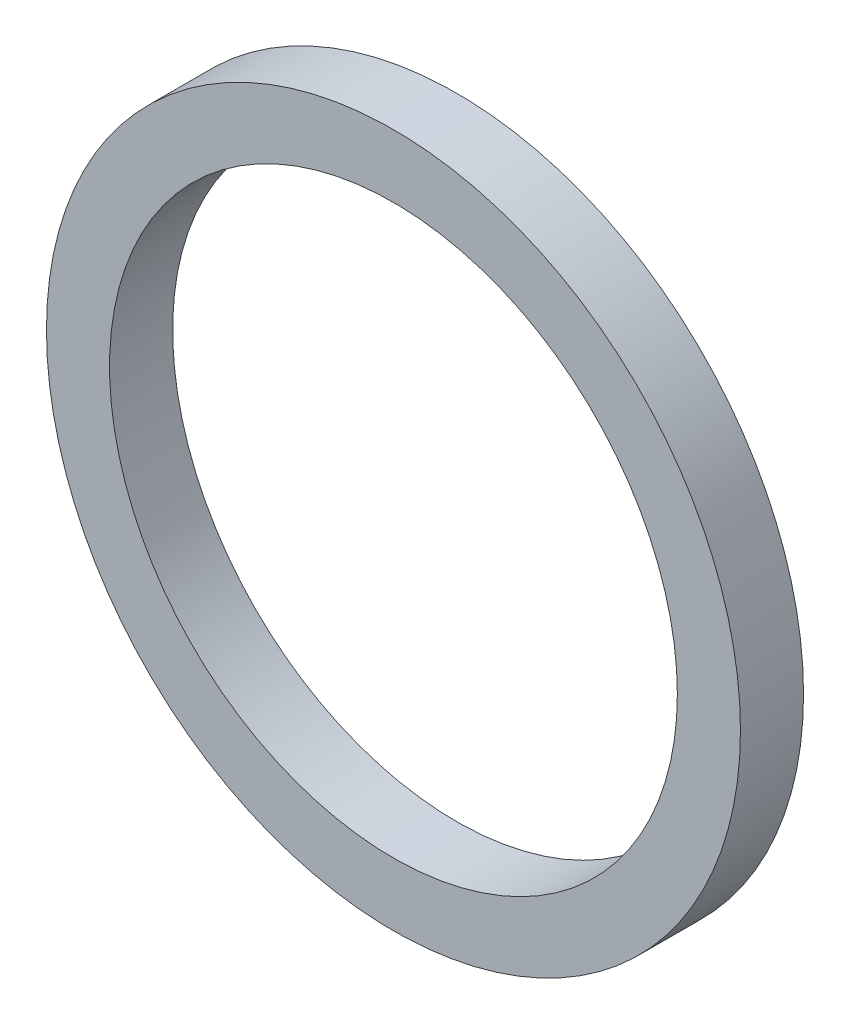
SolidWorks part; units mm, degrees
ref_plane "Front Plane" through (0, 0, 0) normal (0, 0, 1) x (1, 0, 0)
ref_plane "Top Plane" through (0, 0, 0) normal (0, 1, 0) x (1, 0, 0)
ref_plane "Right Plane" through (0, 0, 0) normal (1, 0, 0) x (0, 0, -1)
sketch "Sketch1" plane through (0, 0, 0) normal (0, 0, 1) x (1, 0, 0)
  circle A0 centre (0, 0) radius 4.5
  circle A1 centre (0, 0) radius 5.5
  dimension "D1" = 9
  dimension "D2" = 1
extrude "Boss-Extrude1" add sketch "Sketch1" along normal blind 1
